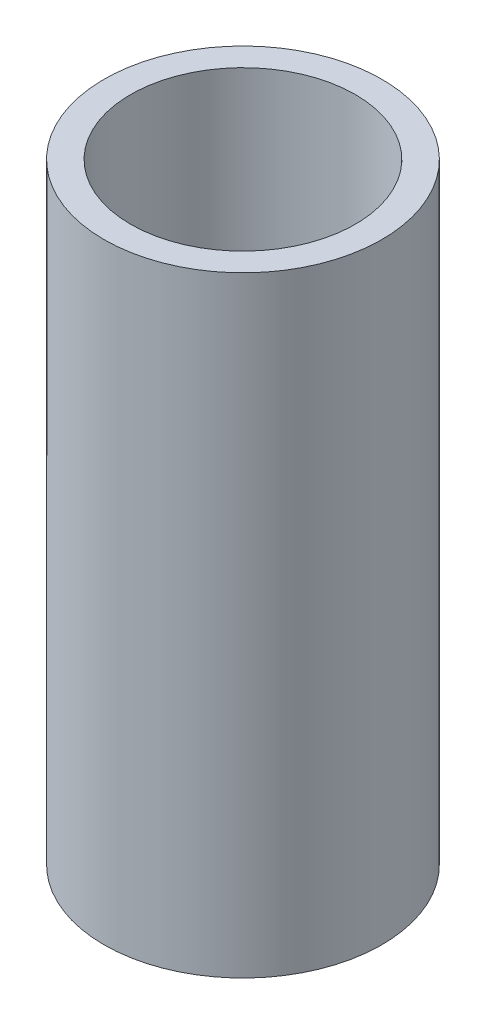
SolidWorks part; units mm, degrees
material "Acrylic (Medium-high impact)"
ref_plane "Front Plane" through (0, 0, 0) normal (0, 0, 1) x (1, 0, 0)
ref_plane "Top Plane" through (0, 0, 0) normal (0, 1, 0) x (1, 0, 0)
ref_plane "Right Plane" through (0, 0, 0) normal (1, 0, 0) x (0, 0, -1)
sketch "Sketch1" plane through (0, 0, 0) normal (0, 1, 0) x (1, 0, 0)
  circle A0 centre (0, 0) radius 28.0416
  circle A1 centre (0, 0) radius 34.6583
  dimension "D1" = 69.3166
  dimension "D2" = 56.0832
extrude "Boss-Extrude1" add sketch "Sketch1" along normal blind 152.4
sketch "Sketch2" plane through (0, 0, 0) normal (0, -1, 0) x (1, 0, 0)
  circle A0 centre (0, 0) radius 28.0416
  circle A1 centre (0, 0) radius 30.7189
  dimension "D1" = 61.4378
extrude "Cut-Extrude1" [suppressed] cut sketch "Sketch2" against normal blind 50.8
sketch "Sketch3" plane through (0, 152.4, 0) normal (0, 1, 0) x (1, 0, 0)
  line L1 (-6.35, 27.3132) -> (6.35, 27.3132)
  line L2 (-6.35, 27.3132) -> (-6.35, 20.9632)
  line L3 (-6.35, 20.9632) -> (6.35, 20.9632)
  line L4 (6.35, 27.3132) -> (6.35, 20.9632)
  circle A0 centre (0, 0) radius 28.0416 construction
  dimension "D1" = 12.7
  dimension "D2" = 6.35
  dimension "D3" = 28.0416
  dimension "D4" = 6.35
extrude "Boss-Extrude3" [suppressed] add sketch "Sketch3" against normal blind 127 separate body
sketch "Sketch4" [suppressed] plane through (0, 0, -20.9632) normal (0, 0, 1) x (1, 0, 0)
  line L0 (6.35, 482.6) -> (-6.35, 482.6)
  line L1 (6.35, 482.6) -> (6.35, 609.6) construction
  line L2 (-6.35, 482.6) -> (-6.35, 495.3)
  line L3 (-6.35, 482.6) -> (-6.35, 609.6) construction
  line L4 (-6.35, 495.3) -> (6.35, 482.6)
  dimension "D1" = 12.7
extrude "Cut-Extrude2" [suppressed] cut sketch "Sketch4" against normal up to next
pattern_circular "CirPattern8" [suppressed] count 2 over 360
equation "\"D2@Sketch3\" = \"D1@Sketch3\"/2"
equation "\"D3@Sketch3\" = \"D2@Sketch1\"/2"
equation "\"D1@Sketch4\" = \"D1@Sketch3\""
